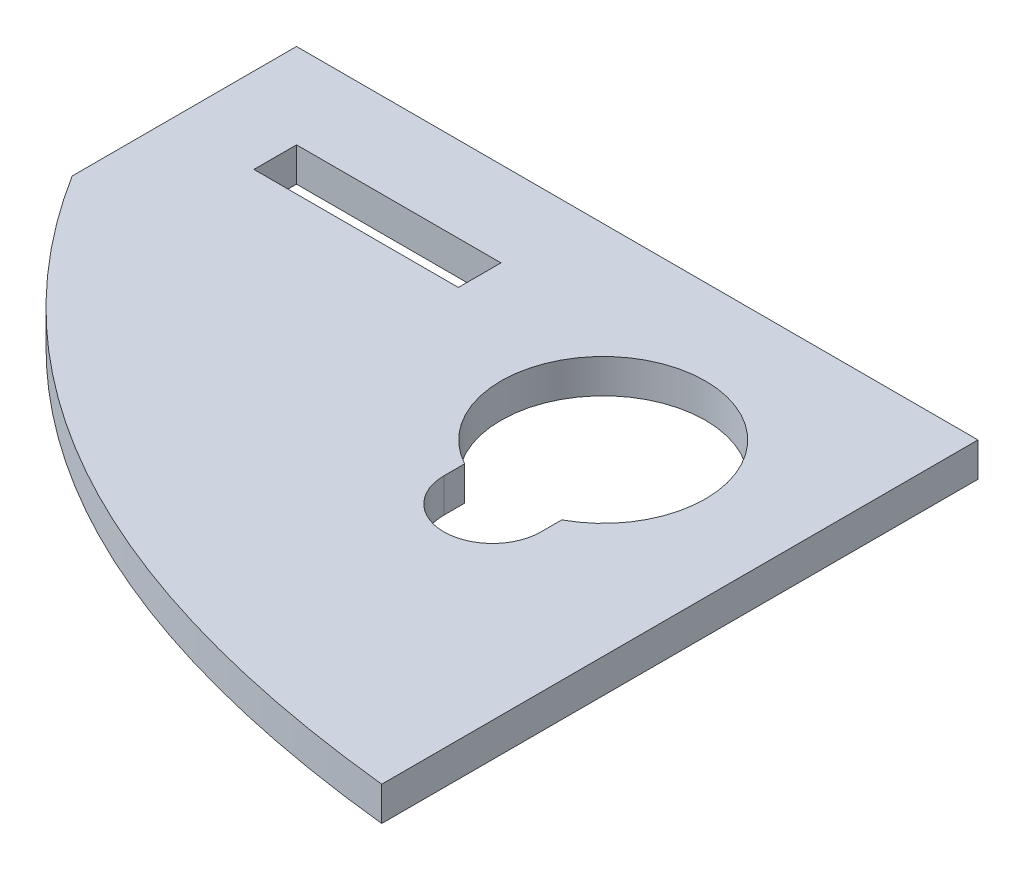
SolidWorks part; units mm, degrees
ref_plane "Plan de face" through (0, 0, 0) normal (0, 0, 1) x (1, 0, 0)
ref_plane "Plan de dessus" through (0, 0, 0) normal (0, 1, 0) x (1, 0, 0)
ref_plane "Plan de droite" through (0, 0, 0) normal (1, 0, 0) x (0, 0, -1)
sketch "Esquisse1" plane through (0, 0, 0) normal (0, 1, 0) x (1, 0, 0)
  line L0 (9, 15.1151) -> (9, -20.8368) construction
  line L1 (-20, -17.5) -> (20, -17.5)
  line L2 (-20, -17.5) -> (-20, 17.5)
  line L3 (-20, 17.5) -> (20, 17.5)
  line L4 (20, -17.5) -> (20, 17.5)
  line L5 (-20, -17.5) -> (20, 17.5) construction
  line L6 (-20, 17.5) -> (20, -17.5) construction
  line L7 (6.15, 1.2201) -> (6.15, 0)
  line L8 (11.85, 1.2201) -> (11.85, 0)
  line L10 (-15, 10) -> (-3, 10)
  line L11 (-15, 10) -> (-15, 12.5)
  line L12 (-15, 12.5) -> (-3, 12.5)
  line L13 (-3, 10) -> (-3, 12.5)
  arc A0 (11.85, 1.2201) -> (6.15, 1.2201) centre (9, 6.5) ccw
  arc A1 (6.15, 0) -> (11.85, 0) centre (9, 0) ccw
  point P0 (0, 0)
  dimension "D1" = 12
  dimension "D2" = 5.7
  dimension "D3" = 6.5
  dimension "D4" = 2.5
  dimension "D5" = 12
  dimension "D6" = 5
  dimension "D7" = 5
  dimension "D8" = 11
  dimension "D9" = 11
  dimension "D10" = 40
  dimension "D11" = 35
extrude "Boss.-Extru.1" add sketch "Esquisse1" along normal blind 2
sketch "Esquisse2" plane through (0, 2, 0) normal (0, 1, 0) x (1, 0, 0)
  line L0 (-20, 17.5) -> (-20, -17.5) construction
  line L1 (-24.0369, 12.4528) -> (-23.502, -22.9175)
  line L2 (-23.502, -22.9175) -> (20, -17.5)
  spline S0 degree 2 poles (20, -17.5) (-13.8368, -13.8982) (-24.0369, 12.4528) knots 0 0 0 1 1 1
extrude "Enlèv. mat.-Extru.1" cut sketch "Esquisse2" against normal blind 10
